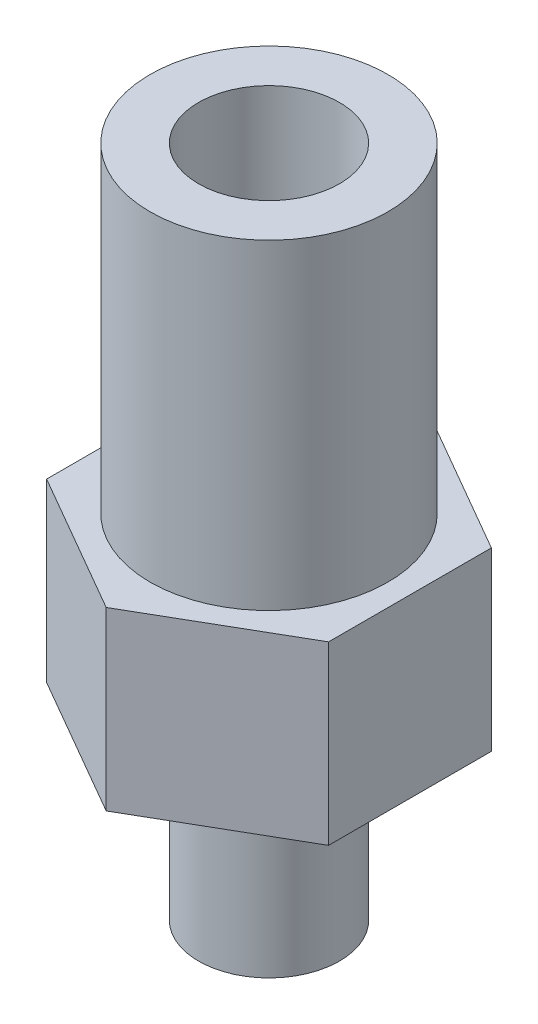
SolidWorks part; units mm, degrees
ref_plane "Front Plane" through (0, 0, 0) normal (0, 0, 1) x (1, 0, 0)
ref_plane "Top Plane" through (0, 0, 0) normal (0, 1, 0) x (1, 0, 0)
ref_plane "Right Plane" through (0, 0, 0) normal (1, 0, 0) x (0, 0, -1)
sketch "Sketch1" plane through (0, 0, 0) normal (0, 1, 0) x (1, 0, 0)
  line L1 (0, 9.2376) -> (-8, 4.6188)
  line L2 (-8, 4.6188) -> (-8, -4.6188)
  line L3 (-8, -4.6188) -> (0, -9.2376)
  line L4 (0, -9.2376) -> (8, -4.6188)
  line L5 (8, -4.6188) -> (8, 4.6188)
  line L6 (8, 4.6188) -> (0, 9.2376)
  circle A0 centre (0, 0) radius 8 construction
  dimension "D1" = 16
extrude "Boss-Extrude1" add sketch "Sketch1" along normal blind 10 contours L5 L6 L1 L2 L3 L4
sketch "Sketch2" plane through (0, 10, 0) normal (0, 1, 0) x (1, 0, 0)
  circle A0 centre (0, 0) radius 6.75
  dimension "D1" = 13.5
extrude "Boss-Extrude2" add sketch "Sketch2" along normal blind 18.2
sketch "Sketch3" plane through (0, 0, 0) normal (0, -1, 0) x (1, 0, 0)
  circle A0 centre (0, 0) radius 4
  dimension "D1" = 8
extrude "Boss-Extrude3" add sketch "Sketch3" along normal blind 10
sketch "Sketch4" plane through (0, 28.2, 0) normal (0, 1, 0) x (1, 0, 0)
  circle A0 centre (0, 0) radius 4
  dimension "D1" = 8
extrude "Cut-Extrude1" cut sketch "Sketch4" against normal blind 26.4
